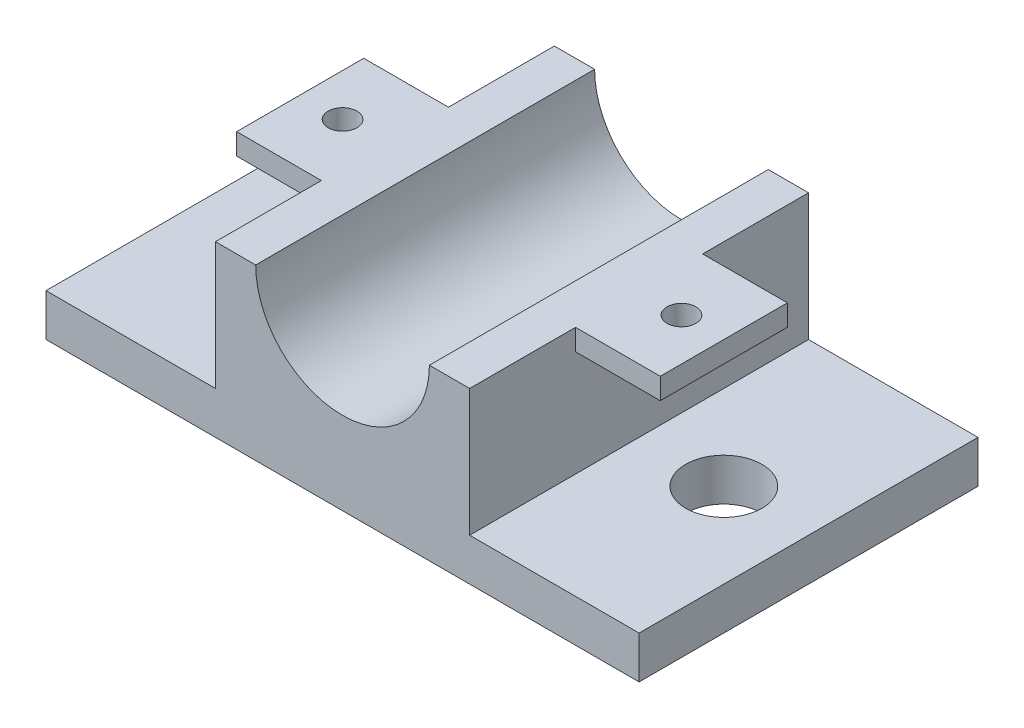
SolidWorks part; units mm, degrees
ref_plane "Front Plane" through (0, 0, 0) normal (0, 0, 1) x (1, 0, 0)
ref_plane "Top Plane" through (0, 0, 0) normal (0, 1, 0) x (1, 0, 0)
ref_plane "Right Plane" through (0, 0, 0) normal (1, 0, 0) x (0, 0, -1)
sketch "Sketch1" plane through (0, 0, 0) normal (0, 1, 0) x (1, 0, 0)
  line L1 (-37.2036, 22.614) -> (32.7964, 22.614)
  line L2 (-37.2036, 22.614) -> (-37.2036, -17.386)
  line L3 (-37.2036, -17.386) -> (32.7964, -17.386)
  line L4 (32.7964, 22.614) -> (32.7964, -17.386)
  dimension "D1" = 40
  dimension "D2" = 70
extrude "Boss-Extrude1" add sketch "Sketch1" along normal blind 5
sketch "Sketch2" plane through (0, 5, 0) normal (0, 1, 0) x (1, 0, 0)
  line L0 (32.7964, 22.614) -> (-37.2036, 22.614) construction
  line L1 (-17.2036, 22.614) -> (12.7964, 22.614)
  line L2 (-17.2036, 22.614) -> (-17.2036, -17.386)
  line L3 (-17.2036, -17.386) -> (12.7964, -17.386)
  line L4 (12.7964, 22.614) -> (12.7964, -17.386)
  line L5 (-37.2036, -17.386) -> (32.7964, -17.386) construction
  point P9 (-2.2036, -17.386)
  point P10 (-2.2036, -17.386)
  dimension "D1" = 30
extrude "Boss-Extrude2" add sketch "Sketch2" along normal blind 15
sketch "Sketch3" plane through (0, 0, 17.386) normal (0, 0, 1) x (1, 0, 0)
  line L0 (-17.2036, 20) -> (12.7964, 20) construction
  circle A0 centre (-2.2036, 20) radius 10.25
  dimension "D1" = 20.5
extrude "Cut-Extrude1" cut sketch "Sketch3" against normal through all
sketch "Sketch5" plane through (0, 20, 0) normal (0, 1, 0) x (1, 0, 0)
  line L0 (-17.2036, 22.614) -> (-17.2036, -17.386) construction
  line L1 (-17.2036, -4.886) -> (-27.2036, -4.886)
  line L2 (-17.2036, -4.886) -> (-17.2036, 10.114)
  line L3 (-17.2036, 10.114) -> (-27.2036, 10.114)
  line L4 (-27.2036, -4.886) -> (-27.2036, 10.114)
  point P6 (-17.2036, 2.614)
  point P7 (-17.2036, 2.614)
  dimension "D1" = 10
  dimension "D2" = 15
extrude "Boss-Extrude3" add sketch "Sketch5" against normal blind 2.5
sketch "Sketch6" plane through (0, 20, 0) normal (0, 1, 0) x (1, 0, 0)
  line L0 (12.7964, -17.386) -> (12.7964, 22.614) construction
  line L1 (12.7964, -4.886) -> (22.7964, -4.886)
  line L2 (12.7964, -4.886) -> (12.7964, 10.114)
  line L3 (12.7964, 10.114) -> (22.7964, 10.114)
  line L4 (22.7964, -4.886) -> (22.7964, 10.114)
  point P6 (12.7964, 2.614)
  point P7 (12.7964, 2.614)
  dimension "D1" = 15
  dimension "D2" = 10
extrude "Boss-Extrude4" add sketch "Sketch6" against normal blind 2.5
hole_wizard "M3 Clearance Hole1" positions "Sketch10" profile "Sketch11" hole size "M3" standard "ANSI Metric" end condition up to next
sketch "Sketch10" plane through (0, 20, 0) normal (0, 1, 0) x (1, 0, 0)
  line L0 (-27.2036, 10.114) -> (-27.2036, -4.886) construction
  line L1 (22.7964, -4.886) -> (22.7964, 10.114) construction
  line L2 (22.7964, 10.114) -> (12.7964, 10.114) construction
  line L3 (-17.2036, 10.114) -> (-27.2036, 10.114) construction
  point P0 (17.7964, 2.614)
  point P2 (-22.2036, 2.614)
  point P10 (-27.2036, 2.614)
  point P13 (22.7964, 2.614)
  point P18 (17.7964, 10.114)
  point P23 (-22.2036, 10.114)
sketch "Sketch11" plane through (17.7964, 20, -2.614) normal (1, 0, 0) x (0, 0, 1)
  line L0 (0, 0) -> (0, 2.5)
  line L1 (0, 2.5) -> (1.7, 2.5)
  line L2 (1.7, 2.5) -> (1.7, 0)
  line L5 (1.7, 0) -> (0, 0)
  line L11 (0, -6.35) -> (0, 107.95) construction
  dimension "Thru Hole Dia." = 3.4
  dimension "Thru Hole Depth" = 2.5
hole_wizard "M8 Clearance Hole1" positions "Sketch12" profile "Sketch13" hole size "M8" standard "ANSI Metric" end condition up to next
sketch "Sketch12" plane through (0, 5, 0) normal (0, 1, 0) x (1, 0, 0)
  line L0 (-37.2036, -17.386) -> (-17.2036, -17.386) construction
  line L1 (12.7964, -17.386) -> (32.7964, -17.386) construction
  line L2 (32.7964, -17.386) -> (32.7964, 22.614) construction
  line L3 (-37.2036, 22.614) -> (-37.2036, -17.386) construction
  point P0 (22.7964, 2.614)
  point P2 (-27.2036, 2.614)
  point P9 (-27.2036, -17.386)
  point P13 (22.7964, -17.386)
  point P17 (32.7964, 2.614)
  point P20 (-37.2036, 2.614)
sketch "Sketch13" plane through (22.7964, 5, -2.614) normal (1, 0, 0) x (0, 0, 1)
  line L0 (0, 0) -> (0, 5)
  line L1 (0, 5) -> (4.5, 5)
  line L2 (4.5, 5) -> (4.5, 0)
  line L5 (4.5, 0) -> (0, 0)
  line L11 (0, -6.35) -> (0, 107.95) construction
  dimension "Thru Hole Dia." = 9
  dimension "Thru Hole Depth" = 5
equation "\"2.5.00mm\"=5"
